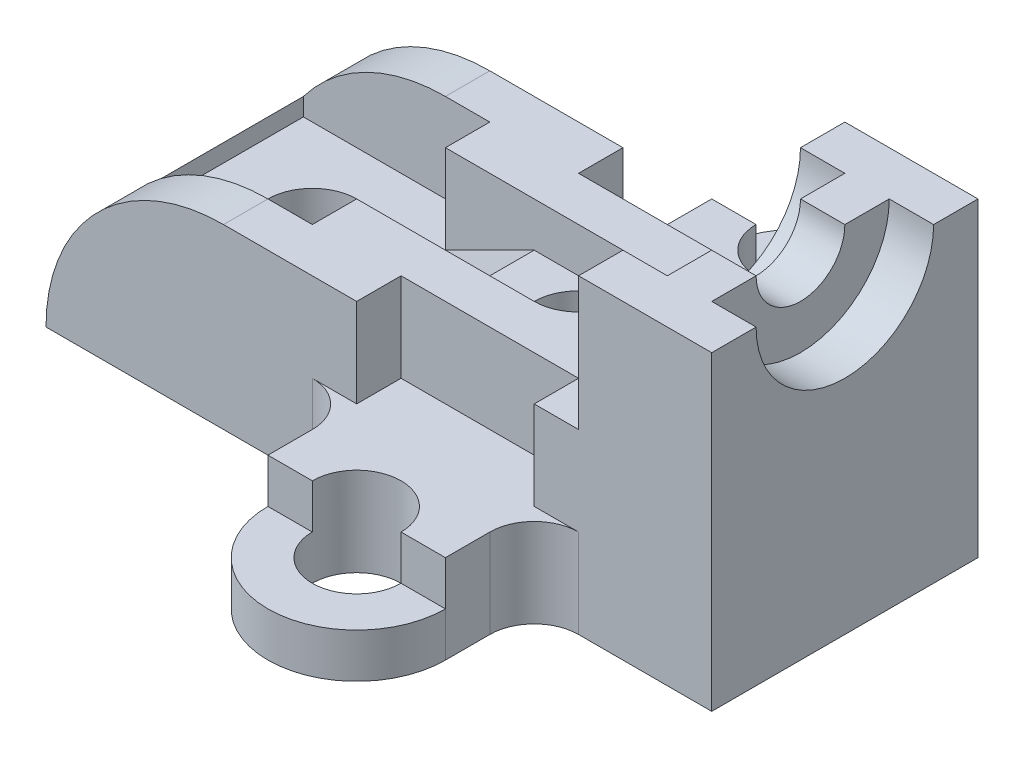
SolidWorks part; units mm, degrees
ref_plane "Front Plane" through (0, 0, 0) normal (0, 0, 1) x (1, 0, 0)
ref_plane "Top Plane" through (0, 0, 0) normal (0, 1, 0) x (1, 0, 0)
ref_plane "Right Plane" through (0, 0, 0) normal (1, 0, 0) x (0, 0, -1)
sketch "Sketch2" plane through (0, 0, 0) normal (0, 0, 1) x (1, 0, 0)
  line L0 (0, 0) -> (150, 0)
  line L1 (150, 0) -> (150, 70)
  line L2 (150, 70) -> (120, 70)
  line L3 (120, 70) -> (120, 40)
  line L4 (120, 40) -> (40, 40)
  arc A0 (40, 40) -> (0, 0) centre (40, 0) ccw
  dimension "D1" = 40
  dimension "D2" = 80
  dimension "D3" = 30
  dimension "D4" = 30
  dimension "D5" = 70
  dimension "D6" = 150
extrude "Boss-Extrude1" add sketch "Sketch2" along normal blind 60
sketch "Sketch4" plane through (150, 0, 0) normal (1, 0, 0) x (0, 0, -1)
  line L0 (-60, 70) -> (0, 70) construction
  line L1 (-50, 70) -> (-40, 70)
  line L2 (-20, 70) -> (-10, 70)
  arc A0 (-10, 70) -> (-50, 70) centre (-30, 70) cw
  arc A1 (-20, 70) -> (-40, 70) centre (-30, 70) cw
  dimension "D1" = 10
  dimension "D2" = 20
extrude "Cut-Extrude1" cut sketch "Sketch4" against normal blind 10
sketch "Sketch5" plane through (120, 0, 0) normal (-1, 0, 0) x (0, 0, 1)
  line L0 (60, 70) -> (0, 70) construction
  line L1 (10, 70) -> (20, 70)
  line L2 (40, 70) -> (50, 70)
  arc A0 (40, 70) -> (20, 70) centre (30, 70) cw
  arc A1 (50, 70) -> (10, 70) centre (30, 70) cw
  dimension "D2" = 10
  dimension "D3" = 20
  dimension "D1" = 10
extrude "Cut-Extrude2" cut sketch "Sketch5" against normal blind 10
sketch "Sketch6" plane through (120, 0, 0) normal (-1, 0, 0) x (0, 0, 1)
  line L0 (40, 70) -> (20, 70) construction
  line L1 (20, 70) -> (40, 70)
  arc A0 (20, 70) -> (40, 70) centre (30, 70) ccw
extrude "Cut-Extrude3" cut sketch "Sketch6" against normal blind 30
sketch "Sketch7" plane through (0, 40, 0) normal (0, 1, 0) x (1, 0, 0)
  line L0 (120, 0) -> (40, 0) construction
  circle A0 centre (90, -30) radius 10
  dimension "D1" = 20
  dimension "D2" = 30
  dimension "D3" = 90
extrude "Cut-Extrude5" cut sketch "Sketch7" against normal blind 75
sketch "Sketch8" plane through (0, 0, 0) normal (0, -1, 0) x (1, 0, 0)
  line L0 (0, 60) -> (150, 60) construction
  line L1 (0, 60) -> (0, 0) construction
  circle A0 centre (30, 30) radius 10
  dimension "D1" = 20
  dimension "D2" = 30
  dimension "D3" = 30
extrude "Cut-Extrude6" cut sketch "Sketch8" against normal blind 75
ref_plane "Plane1" through (0, 20, 0) normal (0, 1, 0) x (1, 0, 0)
sketch "Sketch9" plane through (0, 20, 0) normal (0, 1, 0) x (1, 0, 0)
  line L0 (40, -30) -> (40, 0) construction
  line L1 (50, -10) -> (8, -10)
  line L2 (50, -10) -> (50, -50)
  line L3 (50, -50) -> (8, -50)
  line L4 (8, -10) -> (8, -50)
  dimension "D1" = 40
  dimension "D2" = 10
  dimension "D3" = 10
  dimension "D4" = 42
extrude "Cut-Extrude8" cut sketch "Sketch9" along normal blind 65
sketch "Sketch10" plane through (0, 40, 0) normal (0, 1, 0) x (1, 0, 0)
  line L0 (50, -20) -> (90, -20)
  line L1 (50, -50) -> (50, -10) construction
  line L2 (50, -40) -> (90, -40)
  line L3 (50, -40) -> (50, -20)
  arc A0 (90, -20) -> (90, -40) centre (90, -30) ccw
  circle M1 centre (90, -30) radius 10
  line M3 (50, -10) -> (50, -50)
  dimension "D1" = 20
  dimension "D2" = 10
  dimension "D3" = 40
  dimension "D4" = 40
extrude "Cut-Extrude9" cut sketch "Sketch10" against normal blind 10 contours L2 L0 M3 M1
ref_plane "Plane2" through (0, 0, 20) normal (0, 0, 1) x (1, 0, 0)
sketch "Sketch11" plane through (0, 0, 20) normal (0, 0, 1) x (1, 0, 0)
  line L0 (50, 20) -> (70, 30)
  line L1 (50, 30) -> (90, 30) construction
  line L2 (70, 30) -> (50, 30)
  line L3 (50, 30) -> (50, 20)
  dimension "D1" = 10
  dimension "D2" = 20
  dimension "D3" = 0
extrude "Cut-Extrude10" cut sketch "Sketch11" along normal blind 20
sketch "Sketch12" plane through (0, 40, 0) normal (0, 1, 0) x (1, 0, 0)
  line L0 (120, -60) -> (40, -60) construction
  line L1 (110, -60) -> (70, -60)
  line L2 (110, -60) -> (110, -50)
  line L3 (110, -50) -> (70, -50)
  line L4 (70, -60) -> (70, -50)
  line L5 (120, 0) -> (40, 0) construction
  line L6 (110, 0) -> (70, 0)
  line L7 (110, 0) -> (110, -10)
  line L8 (110, -10) -> (70, -10)
  line L9 (70, 0) -> (70, -10)
  dimension "D1" = 10
  dimension "D2" = 10
  dimension "D3" = 10
  dimension "D4" = 10
  dimension "D5" = 40
  dimension "D6" = 40
extrude "Cut-Extrude11" cut sketch "Sketch12" against normal blind 20
sketch "Sketch13" plane through (0, 0, 0) normal (0, 1, 0) x (1, 0, 0)
  line L0 (0, -60) -> (150, -60) construction
  line L1 (70, -70) -> (70, -80)
  line L2 (110, -70) -> (110, -80)
  line L3 (60, -60) -> (120, -60)
  arc A0 (60, -60) -> (70, -70) centre (60, -70) cw
  arc A1 (120, -60) -> (110, -70) centre (120, -70) ccw
  arc A2 (70, -80) -> (110, -80) centre (90, -80) ccw
  dimension "D1" = 10
  dimension "D2" = 10
  dimension "D6" = 60
  dimension "D8" = 20
  dimension "D3" = 10
  dimension "D4" = 10
  dimension "D7" = 30
extrude "Boss-Extrude2" add sketch "Sketch13" along normal blind 20
sketch "Sketch14" plane through (0, 20, 0) normal (0, 1, 0) x (1, 0, 0)
  line L0 (70, -70) -> (70, -80) construction
  circle A0 centre (90, -80) radius 10
  arc A1 (70, -80) -> (110, -80) centre (90, -80) ccw construction
  point P4 (90, -100)
  dimension "D1" = 20
  dimension "D2" = 20
  dimension "D3" = 20
extrude "Cut-Extrude14" cut sketch "Sketch14" against normal blind 20
sketch "Sketch15" plane through (0, 20, 0) normal (0, 1, 0) x (1, 0, 0)
  line L0 (70, -80) -> (80, -80)
  line L1 (100, -80) -> (110, -80)
  arc A0 (70, -80) -> (110, -80) centre (90, -80) ccw
  arc A1 (70, -80) -> (110, -80) centre (90, -80) ccw construction
  arc A2 (80, -80) -> (100, -80) centre (90, -80) ccw
  circle A3 centre (90, -80) radius 10 construction
extrude "Cut-Extrude15" cut sketch "Sketch15" against normal blind 10
sketch "Sketch17" plane through (0, 0, 0) normal (0, -1, 0) x (1, 0, 0)
  line L0 (0, 0) -> (150, 0) construction
  line L1 (110, -10) -> (110, -20)
  line L2 (70, -10) -> (70, -20)
  line L3 (120, 0) -> (60, 0)
  line L4 (70, 0) -> (70, 10) construction
  arc A0 (120, 0) -> (110, -10) centre (120, -10) ccw
  arc A1 (60, 0) -> (70, -10) centre (60, -10) cw
  arc A2 (110, -20) -> (70, -20) centre (90, -20) cw
  point P11 (70, 5)
  dimension "D3" = 20
  dimension "D4" = 10
  dimension "D5" = 10
  dimension "D1" = 30
  dimension "D2" = 60
  dimension "D6" = 10
  dimension "D7" = 10
  dimension "D8" = 10
  dimension "D9" = 10
extrude "Boss-Extrude3" add sketch "Sketch17" against normal blind 20
sketch "Sketch18" plane through (0, 20, 0) normal (0, 1, 0) x (1, 0, 0)
  line L0 (110, 20) -> (110, 10) construction
  circle A0 centre (90, 20) radius 10
  arc A1 (110, 20) -> (70, 20) centre (90, 20) ccw construction
  point P2 (110, 15)
  point P5 (90, 40)
  dimension "D1" = 20
  dimension "D2" = 20
  dimension "D3" = 20
extrude "Cut-Extrude16" cut sketch "Sketch18" against normal blind 20
sketch "Sketch19" plane through (0, 20, 0) normal (0, 1, 0) x (1, 0, 0)
  line L0 (100, 20) -> (110, 20)
  line L1 (80, 20) -> (70, 20)
  arc A0 (100, 20) -> (80, 20) centre (90, 20) ccw
  circle A1 centre (90, 20) radius 10 construction
  arc A2 (110, 20) -> (70, 20) centre (90, 20) ccw
  arc A3 (110, 20) -> (70, 20) centre (90, 20) ccw construction
  dimension "D1" = 10
  dimension "D2" = 10
extrude "Cut-Extrude17" cut sketch "Sketch19" against normal blind 10
